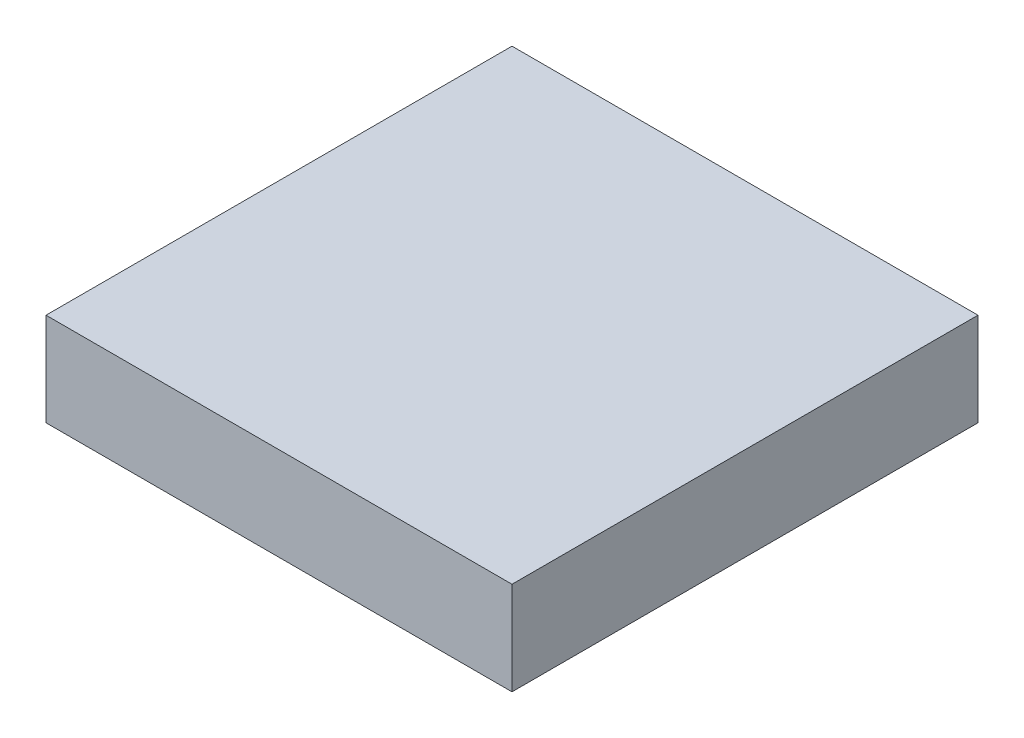
SolidWorks part; units mm, degrees
ref_plane "Front Plane" through (0, 0, 0) normal (0, 0, 1) x (1, 0, 0)
ref_plane "Top Plane" through (0, 0, 0) normal (0, 1, 0) x (1, 0, 0)
ref_plane "Right Plane" through (0, 0, 0) normal (1, 0, 0) x (0, 0, -1)
sketch "Sketch1" plane through (0, 0, 0) normal (0, 1, 0) x (1, 0, 0)
  line L0 (0, 0) -> (18.6879, 0) construction
  line L1 (0, 0) -> (0, -14.4281) construction
  line L3 (-1, 1) -> (1, 1)
  line L4 (-1, 1) -> (-1, -1)
  line L5 (-1, -1) -> (1, -1)
  line L6 (1, 1) -> (1, -1)
  dimension "D1" = 2
  dimension "D2" = 2
extrude "Boss-Extrude1" add sketch "Sketch1" along normal blind 0.4
